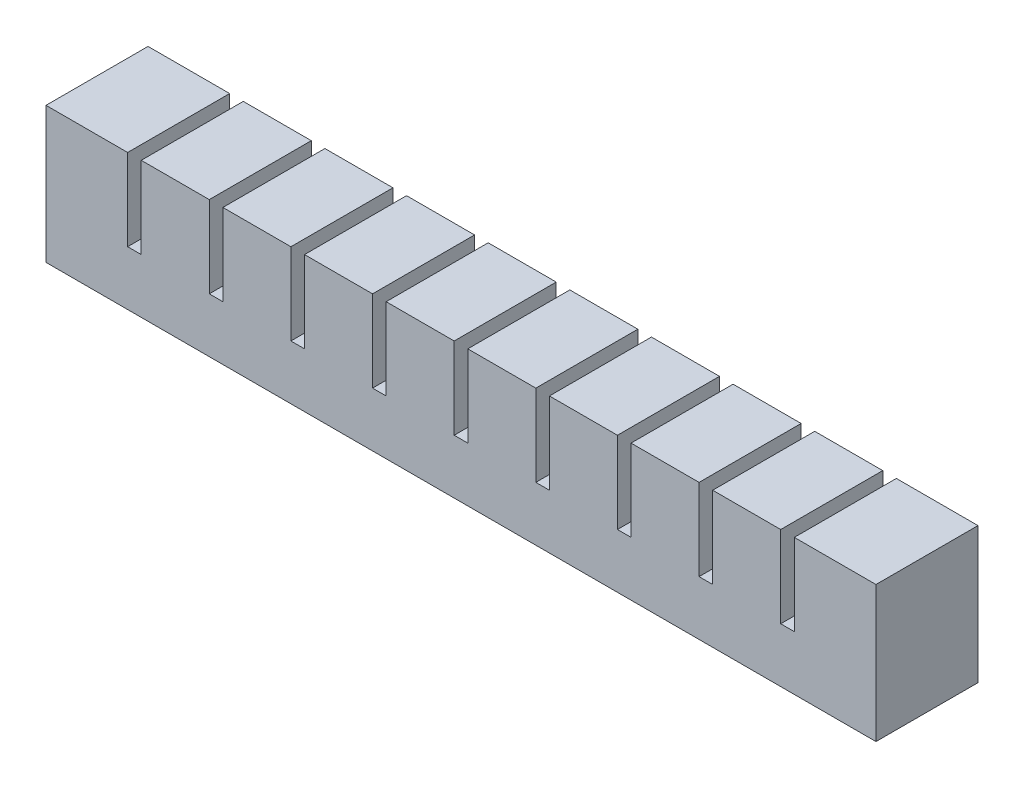
SolidWorks part; units mm, degrees
ref_plane "Front Plane" through (0, 0, 0) normal (0, 0, 1) x (1, 0, 0)
ref_plane "Top Plane" through (0, 0, 0) normal (0, 1, 0) x (1, 0, 0)
ref_plane "Right Plane" through (0, 0, 0) normal (1, 0, 0) x (0, 0, -1)
sketch "Sketch1" plane through (0, 0, 0) normal (0, 0, 1) x (1, 0, 0)
  line L1 (0, 0) -> (10, 0)
  line L2 (0, 0) -> (0, 15)
  line L3 (0, 15) -> (10, 15)
  line L4 (10, 0) -> (10, 15)
  dimension "D1" = 10
  dimension "D2" = 15
extrude "Boss-Extrude1" add sketch "Sketch1" along normal blind 15
sketch "Sketch2" plane through (0, 0, 0) normal (0, -1, 0) x (1, 0, 0)
  line L0 (0, 15) -> (10, 15) construction
  line L1 (3, 12) -> (7, 12)
  line L2 (3, 12) -> (3, 3)
  line L3 (3, 3) -> (7, 3)
  line L4 (7, 12) -> (7, 3)
  line L5 (10, 15) -> (10, 0) construction
  line L6 (0, 0) -> (10, 0) construction
  line L7 (0, 15) -> (0, 0) construction
  dimension "D1" = 3
  dimension "D2" = 3
  dimension "D3" = 3
  dimension "D4" = 3
extrude "Cut-Extrude1" cut sketch "Sketch2" against normal blind 12
sketch "Sketch3" plane through (10, 0, 0) normal (1, 0, 0) x (0, 0, -1)
  line L0 (0, 0) -> (0, 15) construction
  line L1 (-15, 0) -> (0, 0)
  line L2 (-15, 0) -> (-15, 3)
  line L3 (-15, 3) -> (0, 3)
  line L4 (0, 0) -> (0, 3)
  dimension "D1" = 3
extrude "Boss-Extrude2" add sketch "Sketch3" along normal blind 2
pattern_linear "LPattern1" count 10 spacing 12 along (1, 0, 0) of bodies 103
combine bodies "Combine1" operation type add bodies to combine 112 104 105 106 107 108 103 109 110 111
sketch "Sketch4" plane through (118, 0, 0) normal (1, 0, 0) x (0, 0, -1)
  line L1 (-15, 3) -> (0, 3)
  line L2 (-15, 3) -> (-15, 15)
  line L3 (-15, 15) -> (0, 15)
  line L4 (0, 3) -> (0, 15)
extrude "Boss-Extrude3" add sketch "Sketch4" along normal up to surface (2 mm away) up to face at (120, 1.5, 7.5)
sketch "Sketch5" plane through (0, 0, 0) normal (-1, 0, 0) x (0, 0, 1)
  line L1 (0, 15) -> (15, 15)
  line L2 (0, 15) -> (0, 0)
  line L3 (0, 0) -> (15, 0)
  line L4 (15, 15) -> (15, 0)
extrude "Boss-Extrude4" add sketch "Sketch5" along normal blind 2
ref_point "Point1"
sketch "Sketch6" plane through (0, 0, 0) normal (0, -1, 0) x (1, 0, 0)
  line L0 (111, 12) -> (111, 3) construction
  line L1 (7, 9) -> (111, 9)
  line L2 (7, 9) -> (7, 6)
  line L3 (7, 6) -> (111, 6)
  line L4 (111, 9) -> (111, 6)
  line L5 (7, 9) -> (111, 6) construction
  line L6 (7, 6) -> (111, 9) construction
  point P0 (59, 7.5)
  dimension "D1" = 3
extrude "Cut-Extrude2" cut sketch "Sketch6" against normal blind 2.5
sketch "Sketch7" plane through (0, 0, 0) normal (0, -1, 0) x (1, 0, 0)
  line L1 (-2, 15) -> (120, 15)
  line L2 (-2, 15) -> (-2, 0)
  line L3 (-2, 0) -> (120, 0)
  line L4 (120, 15) -> (120, 0)
extrude "Boss-Extrude5" add sketch "Sketch7" along normal blind 3
sketch "Sketch8" plane through (0, -3, 0) normal (0, -1, 0) x (1, 0, 0)
  line L1 (-2, 15) -> (120, 15)
  line L2 (-2, 15) -> (-2, 0)
  line L3 (-2, 0) -> (120, 0)
  line L4 (120, 15) -> (120, 0)
extrude "Boss-Extrude6" add sketch "Sketch8" along normal blind 2
